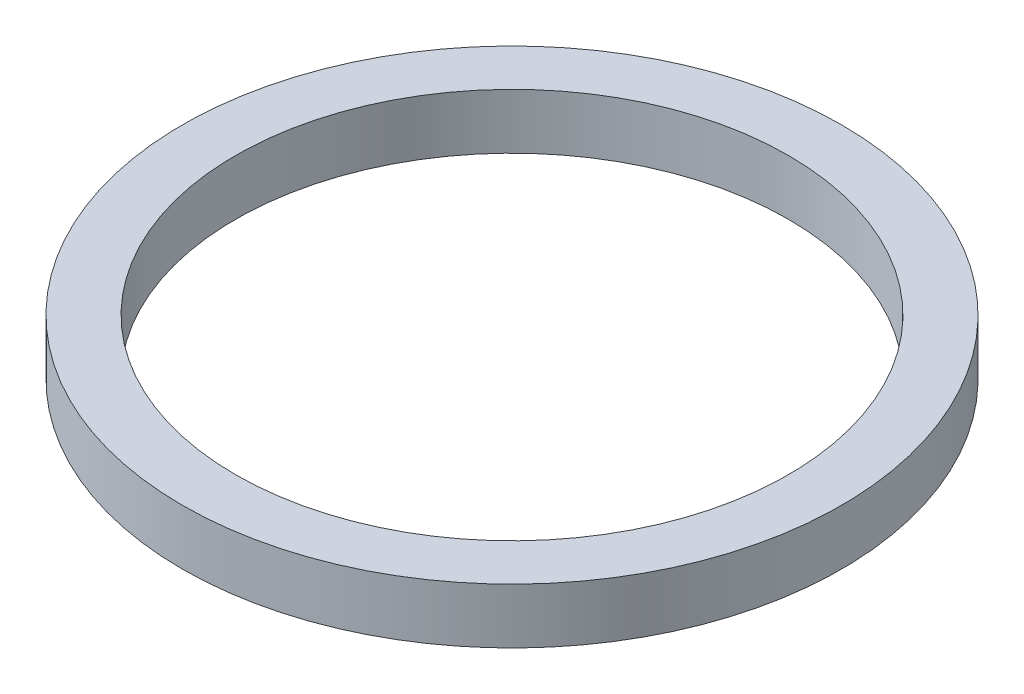
SolidWorks part; units mm, degrees
ref_plane "Front Plane" through (0, 0, 0) normal (0, 0, 1) x (1, 0, 0)
ref_plane "Top Plane" through (0, 0, 0) normal (0, 1, 0) x (1, 0, 0)
ref_plane "Right Plane" through (0, 0, 0) normal (1, 0, 0) x (0, 0, -1)
sketch "Sketch1" plane through (0, 0, 0) normal (0, 1, 0) x (1, 0, 0)
  circle A0 centre (0, 0) radius 7.9375
  circle A1 centre (0, 0) radius 9.4615
  dimension "D1" = 15.875
  dimension "D2" = 18.923
extrude "Boss-Extrude1" add sketch "Sketch1" along normal blind 1.5875
